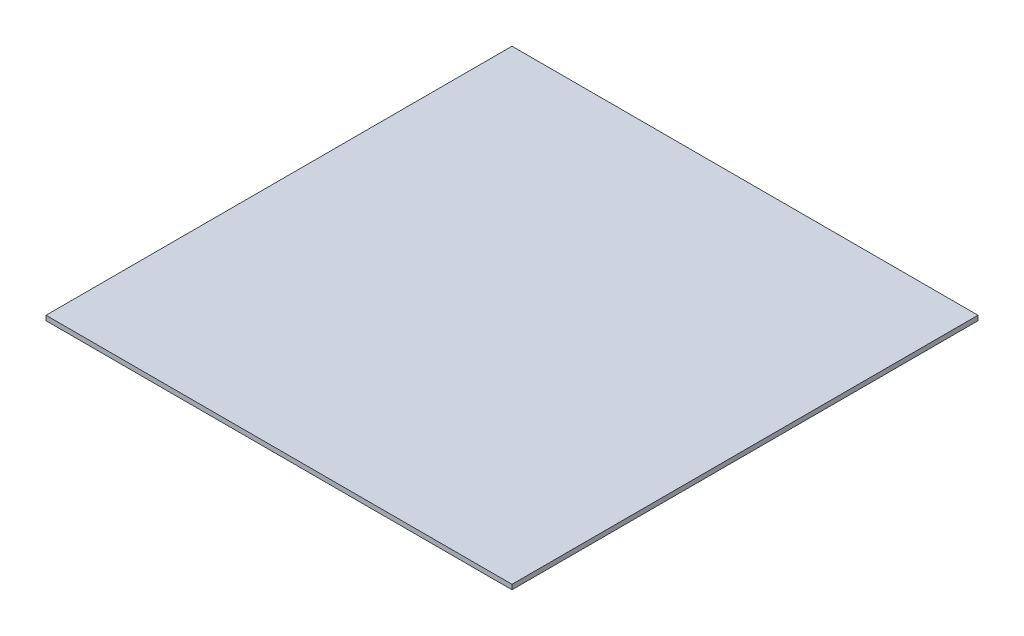
SolidWorks part; units mm, degrees
ref_plane "Front Plane" through (0, 0, 0) normal (0, 0, 1) x (1, 0, 0)
ref_plane "Top Plane" through (0, 0, 0) normal (0, 1, 0) x (1, 0, 0)
ref_plane "Right Plane" through (0, 0, 0) normal (1, 0, 0) x (0, 0, -1)
sketch "Sketch1" plane through (0, 0, 0) normal (0, 1, 0) x (1, 0, 0)
  line L1 (146.05, -146.05) -> (-146.05, -146.05)
  line L2 (146.05, -146.05) -> (146.05, 146.05)
  line L3 (146.05, 146.05) -> (-146.05, 146.05)
  line L4 (-146.05, -146.05) -> (-146.05, 146.05)
  line L5 (146.05, -146.05) -> (-146.05, 146.05) construction
  line L6 (146.05, 146.05) -> (-146.05, -146.05) construction
  point P0 (0, 0)
  dimension "D1" = 292.1
  dimension "D2" = 292.1
extrude "Boss-Extrude1" add sketch "Sketch1" along normal blind 3
